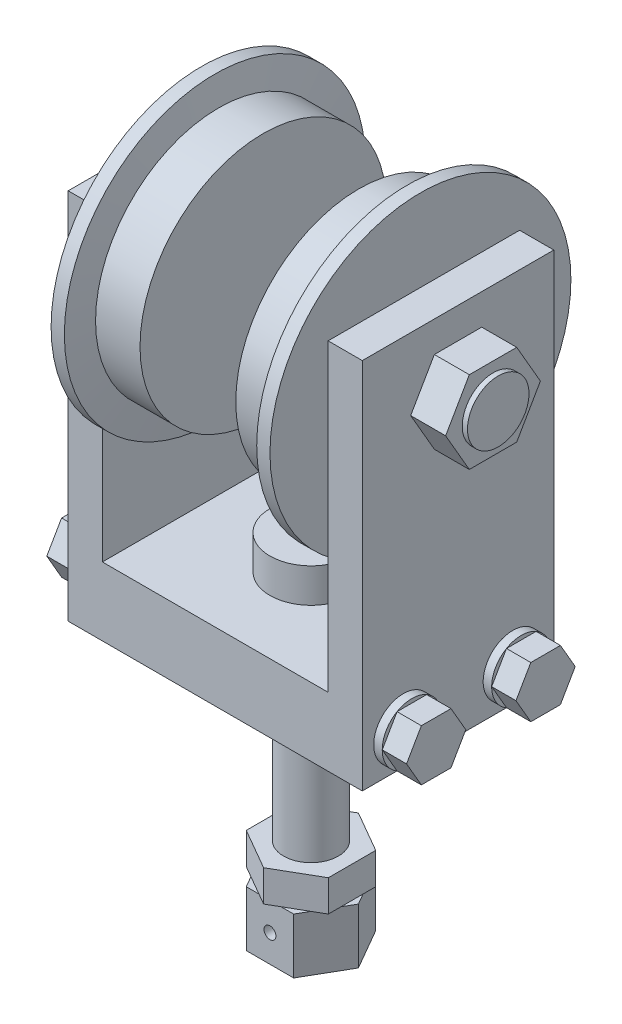
SolidWorks part; units mm, degrees
ref_plane "Front" through (0, 0, 0) normal (0, 0, 1) x (1, 0, 0)
ref_plane "Top" through (0, 0, 0) normal (0, 1, 0) x (1, 0, 0)
ref_plane "Right" through (0, 0, 0) normal (1, 0, 0) x (0, 0, -1)
ref_plane "Z PLANE" through (0, 0, 0) normal (0, 0, 1) x (1, 0, 0)
ref_plane "YOKE BOTTOM" through (0, 0, 0) normal (0, 1, 0) x (-1, 0, 0)
ref_plane "X PLANE" through (0, 0, 0) normal (1, 0, 0) x (0, 0, -1)
sketch "YOKE CROSS SECTION" plane through (0, 0, 0) normal (1, 0, 0) x (0, 0, -1)
  line L0 (0, 0) -> (0, 57.0916) construction
  line L1 (0, 84.8167) -> (0, -84.8167) construction
  line L2 (-44.45, 0) -> (44.45, 0)
  line L3 (69.1602, 0) -> (-69.1602, 0) construction
  line L4 (44.45, 0) -> (44.45, 31.75)
  line L5 (-44.45, 0) -> (-44.45, 31.75)
  line L6 (44.45, 31.75) -> (-44.45, 31.75)
  point P12 (0, 31.75)
  dimension "D1" = 31.75
  dimension "D2" = 88.9
ref_plane "1/2 YOKE LENGTH (A)" through (52.3875, 0, 0) normal (1, 0, 0) x (0, 0, -1)
extrude "YOKE" add sketch "YOKE CROSS SECTION" along normal up to surface (52.3875 mm away) up to plane "1/2 YOKE LENGTH (A)"
sketch "SIDEPLATE PROFILE" plane through (52.3875, 0, 0) normal (1, 0, 0) x (0, 0, -1)
  line L0 (0, 0) -> (0, 74.7424) construction
  line L1 (0, 85.6885) -> (0, -85.6885) construction
  line L2 (-44.45, 0) -> (44.45, 0)
  line L3 (44.45, 0) -> (44.45, 173.0375)
  line L4 (-44.45, 0) -> (-44.45, 173.0375)
  line L5 (44.45, 173.0375) -> (-44.45, 173.0375)
  point P11 (0, 173.0375)
  dimension "D1" = 173.0375
ref_plane "WHEEL HEIGHT" through (0, 139.7, 0) normal (0, 1, 0) x (-1, 0, 0)
ref_plane "SCREW LOCATION X" through (0, 0, 25.4) normal (0, 0, 1) x (1, 0, 0)
ref_plane "SCREW LOCATION Y" through (0, 15.875, 0) normal (0, 1, 0) x (-1, 0, 0)
extrude "SIDEPLATE" add sketch "SIDEPLATE PROFILE" along normal blind 15.875
sketch "WHEEL PIN NUT PROFILE" plane through (68.2625, 0, 0) normal (1, 0, 0) x (0, 0, -1)
  line L0 (0, 85.6885) -> (0, -85.6885) construction
  line L1 (21.997, 139.7) -> (10.9985, 158.75)
  line L2 (10.9985, 158.75) -> (-10.9985, 158.75)
  line L3 (-10.9985, 158.75) -> (-21.997, 139.7)
  line L4 (-21.997, 139.7) -> (-10.9985, 120.65)
  line L5 (-10.9985, 120.65) -> (10.9985, 120.65)
  line L6 (10.9985, 120.65) -> (21.997, 139.7)
  line L7 (69.1602, 139.7) -> (-69.1602, 139.7) construction
  circle A0 centre (0, 139.7) radius 19.05 construction
  dimension "D1" = 38.1
extrude "WHEEL PIN NUT" add sketch "WHEEL PIN NUT PROFILE" along normal blind 16.2306
sketch "WHEEL PIN PROJECTION PROFILE" plane through (84.4931, 0, 0) normal (1, 0, 0) x (0, 0, -1)
  line L0 (0, 85.6885) -> (0, -85.6885) construction
  line L1 (69.1602, 139.7) -> (-69.1602, 139.7) construction
  circle A0 centre (0, 139.7) radius 14.2875
  dimension "D1" = 28.575
extrude "WHEEL PIN PROJECTION" add sketch "WHEEL PIN PROJECTION PROFILE" along normal blind 2.413
sketch "LOCKNUTS PROFILE" plane through (68.2625, 0, 0) normal (1, 0, 0) x (0, 0, -1)
  line L0 (-25.4, 84.8167) -> (-25.4, -84.8167) construction
  line L1 (50, 15.875) -> (-50, 15.875) construction
  circle A0 centre (-25.4, 15.875) radius 13.7541
  dimension "D1" = 27.5082
extrude "LOCKNUTS" add sketch "LOCKNUTS PROFILE" along normal blind 3.9624
sketch "SCREWS PROFILE" plane through (72.2249, 0, 0) normal (1, 0, 0) x (0, 0, -1)
  line L0 (50, 15.875) -> (-50, 15.875) construction
  line L1 (-11.6518, 15.875) -> (-18.5259, 27.7812)
  line L2 (-18.5259, 27.7812) -> (-32.2741, 27.7812)
  line L3 (-32.2741, 27.7812) -> (-39.1482, 15.875)
  line L4 (-39.1482, 15.875) -> (-32.2741, 3.9688)
  line L5 (-32.2741, 3.9688) -> (-18.5259, 3.9688)
  line L6 (-18.5259, 3.9688) -> (-11.6518, 15.875)
  line L7 (-25.4, 84.8167) -> (-25.4, -84.8167) construction
  circle A0 centre (-25.4, 15.875) radius 11.9062 construction
  dimension "D1" = 23.8125
extrude "SCREWS" add sketch "SCREWS PROFILE" along normal blind 11.2776
sketch "PROFILE" plane through (0, 31.75, 0) normal (0, 1, 0) x (-1, 0, 0)
  line L0 (85.6885, 0) -> (-85.6885, 0) construction
  line L1 (0, 82.9507) -> (0, -82.9507) construction
  circle A0 centre (0, 0) radius 19.05
  dimension "D1" = 38.1
extrude "KING BOLT HEAD" add sketch "PROFILE" along normal blind 15.875
mirror "Mirror1" about plane through (0, 0, 0) normal (0, 0, 1) of "SCREWS", "LOCKNUTS"
mirror "Mirror5" about plane through (0, 0, 0) normal (1, 0, 0) of bodies 112
ref_plane "TOP OF NUT" through (0, -76.2, 0) normal (0, 1, 0) x (-1, 0, 0)
sketch "DIA." plane through (0, 0, 0) normal (0, -1, 0) x (1, 0, 0)
  line L0 (85.6885, 0) -> (-85.6885, 0) construction
  line L1 (0, -82.9507) -> (0, 82.9507) construction
  circle A0 centre (0, 0) radius 12.7
  dimension "D1" = 25.4
extrude "KING BOLT" add sketch "DIA." along normal up to surface (76.2 mm away) up to plane "TOP OF NUT"
sketch "KING BOLT JAN NUT PROFILE" plane through (0, -76.2, 0) normal (0, -1, 0) x (1, 0, 0)
  line L0 (85.6885, 0) -> (-85.6885, 0) construction
  line L1 (0, -21.997) -> (19.05, -10.9985)
  line L2 (19.05, -10.9985) -> (19.05, 10.9985)
  line L3 (19.05, 10.9985) -> (0, 21.997)
  line L4 (0, 21.997) -> (-19.05, 10.9985)
  line L5 (-19.05, 10.9985) -> (-19.05, -10.9985)
  line L6 (-19.05, -10.9985) -> (0, -21.997)
  line L7 (0, -82.9507) -> (0, 82.9507) construction
  circle A0 centre (0, 0) radius 19.05 construction
  dimension "D1" = 38.1
extrude "KING BOLT JAM NUT" add sketch "KING BOLT JAN NUT PROFILE" along normal blind 14.605
sketch "KING BOLT NUT PROFILE" plane through (0, -90.805, 0) normal (0, -1, 0) x (1, 0, 0)
  line L1 (21.997, 0) -> (10.9985, 19.05)
  line L2 (10.9985, 19.05) -> (-10.9985, 19.05)
  line L3 (-10.9985, 19.05) -> (-21.997, 0)
  line L4 (-21.997, 0) -> (-10.9985, -19.05)
  line L5 (-10.9985, -19.05) -> (10.9985, -19.05)
  line L6 (10.9985, -19.05) -> (21.997, 0)
  line L10 (0, -82.9507) -> (0, 82.9507) construction
  line L11 (85.6885, 0) -> (-85.6885, 0) construction
  circle A0 centre (0, 0) radius 19.05 construction
  dimension "D1" = 38.1
extrude "KING BOLT NUT" add sketch "KING BOLT NUT PROFILE" along normal blind 25.7048
sketch "Sketch5" plane through (0, -116.5098, 0) normal (0, -1, 0) x (1, 0, 0)
  circle A0 centre (0, 0) radius 12.7 construction
  circle A1 centre (0, 0) radius 12.7
extrude "EXTENDED KING BOLT" add sketch "Sketch5" along normal blind 6.35
chamfer "Chamfer1" distance 2.3812 angle 45 1 edges at (0, -122.8598, -12.7)
ref_plane "MOUNTING REF PLANE" through (0, -34.925, 0) normal (0, 1, 0) x (-1, 0, 0)
sketch "Sketch7" plane through (0, 0, 0) normal (0, 0, 1) x (1, 0, 0)
  line L0 (50.8, 155.575) -> (50.8, 209.55)
  line L1 (42.8625, 196.85) -> (44.6474, 209.55)
  line L2 (52.3875, 139.7) -> (22.225, 139.7)
  line L3 (42.8625, 196.85) -> (22.225, 196.85)
  line L4 (22.225, 139.7) -> (22.225, 196.85)
  line L5 (52.3875, 139.7) -> (52.3875, 155.575)
  line L6 (52.3875, 155.575) -> (50.8, 155.575)
  line L7 (50.8, 209.55) -> (44.6474, 209.55)
  line L8 (69.1602, 139.7) -> (-69.1602, 139.7) construction
  line L10 (52.3875, -75.0522) -> (52.3875, 75.0522) construction
  dimension "D3" = 69.85
  dimension "D1" = 57.15
  dimension "D2" = 15.875
  dimension "D4" = 1.5875
  dimension "D5" = 7.7401
  dimension "D6" = 9.525
  dimension "D7" = 30.1625
revolve "WHEEL" add sketch "Sketch7" angle 360 about axis through (86.9061, 139.7, 0) along (-1, 0, 0)
mirror "Mirror6" about plane through (0, 0, 0) normal (1, 0, 0) of "WHEEL"
sketch "Sketch8" plane through (0, 0, 19.05) normal (0, 0, 1) x (1, 0, 0)
  line L0 (0, -82.9507) -> (0, 82.9507) construction
  line L1 (-10.9985, -116.5098) -> (-21.997, -116.5098) construction
  circle A0 centre (0, -103.8098) radius 2.7686
  dimension "D2" = 5.5372
  dimension "D1" = 12.7
extrude "COTTER PIN HOLE" cut sketch "Sketch8" against normal up to next
sketch "Sketch9" plane through (0, 0, 0) normal (0, -1, 0) x (1, 0, 0)
  circle A0 centre (0, 0) radius 25.4
  circle A1 centre (0, 0) radius 30.1625
  dimension "D1" = 50.8
  dimension "D2" = 60.325
extrude "SPACER" [suppressed] add sketch "Sketch9" along normal blind 12.7
ref_plane "TREAD OF TRACK" through (0, 82.55, 0) normal (0, 1, 0) x (-1, 0, 0)
